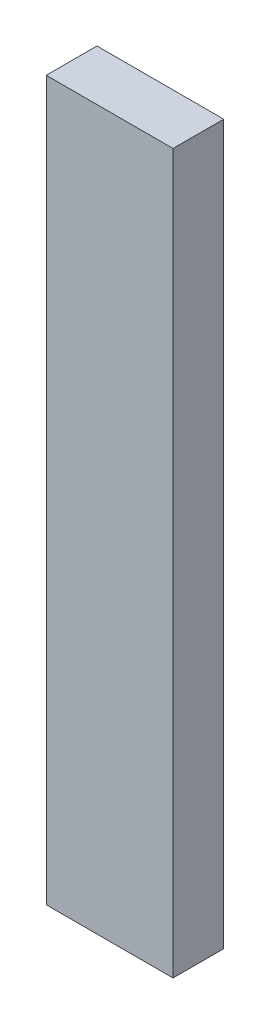
SolidWorks part; units mm, degrees
ref_plane "Plan de face" through (0, 0, 0) normal (0, 0, 1) x (1, 0, 0)
ref_plane "Plan de dessus" through (0, 0, 0) normal (0, 1, 0) x (1, 0, 0)
ref_plane "Plan de droite" through (0, 0, 0) normal (1, 0, 0) x (0, 0, -1)
sketch "Esquisse1" plane through (0, 0, 0) normal (0, 0, 1) x (1, 0, 0)
  line L1 (-7.5, 42.5) -> (7.5, 42.5)
  line L2 (-7.5, 42.5) -> (-7.5, -42.5)
  line L3 (-7.5, -42.5) -> (7.5, -42.5)
  line L4 (7.5, 42.5) -> (7.5, -42.5)
  dimension "D1" = 85
  dimension "D2" = 15
  dimension "D3" = 7.5
  dimension "D4" = 42.5
extrude "Boss.-Extru.1" add sketch "Esquisse1" along normal blind 6
equation "\"D3@Esquisse1\"=\"D2@Esquisse1\"/2"
equation "\"D4@Esquisse1\"=\"D1@Esquisse1\"/2"
